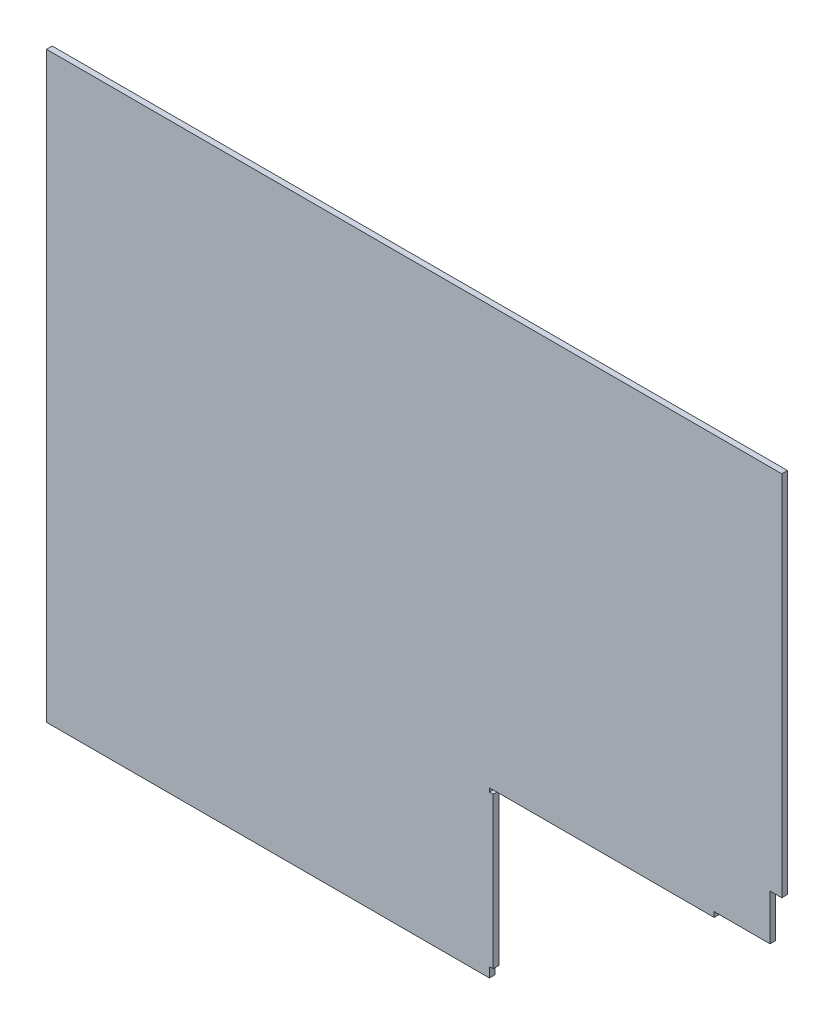
SolidWorks part; units mm, degrees
material "Acrylic (Medium-high impact)"
ref_plane "Front Plane" through (0, 0, 0) normal (0, 0, 1) x (1, 0, 0)
ref_plane "Top Plane" through (0, 0, 0) normal (0, 1, 0) x (1, 0, 0)
ref_plane "Right Plane" through (0, 0, 0) normal (1, 0, 0) x (0, 0, -1)
sketch "Sketch1" plane through (0, 0, 0) normal (0, 0, 1) x (1, 0, 0)
  line L1 (-289.5, -229.5) -> (289.5, -229.5)
  line L2 (-289.5, -229.5) -> (-289.5, 229.5)
  line L3 (-289.5, 229.5) -> (289.5, 229.5)
  line L4 (289.5, -229.5) -> (289.5, 229.5)
  line L5 (-289.5, -229.5) -> (289.5, 229.5) construction
  line L6 (-289.5, 229.5) -> (289.5, -229.5) construction
  point P0 (0, 0)
  dimension "D1" = 579
  dimension "D2" = 459
extrude "Boss-Extrude1" add sketch "Sketch1" along normal mid plane 4.4958
sketch "Sketch2" plane through (0, 0, -2.2479) normal (0, 0, -1) x (-1, 0, 0)
  line L0 (-275.0972, -60.2) -> (-283.75, -60.2) construction
  line L1 (-280.75, -96.2) -> (-280.75, -61.2) construction
  line L2 (-252.237, -96.2) -> (-280.75, -96.2) construction
  line L3 (-236.75, -97.2) -> (-236.75, -99.2) construction
  line L4 (-60.75, -100.2) -> (-283.75, -100.2) construction
  line L5 (-59.75, -100.2) -> (-59.75, -102.2) construction
  line L6 (-60.75, -102.2) -> (-283.75, -102.2) construction
  line L7 (-62.75, -102.45) -> (-62.75, -221.95) construction
  line L8 (-283.75, -222.2) -> (-60.75, -222.2) construction
  line L9 (-59.75, -222.2) -> (-59.75, -224.2) construction
  line L10 (-280.75, -60.2) -> (-289.5, -60.2) construction
  line L11 (-280.75, -96.2) -> (-280.75, -60.2) construction
  line L12 (-236.75, -96.2) -> (-280.75, -96.2) construction
  line L13 (-236.75, -96.2) -> (-236.75, -100.2) construction
  line L14 (-59.75, -100.2) -> (-236.75, -100.2) construction
  line L15 (-59.75, -100.2) -> (-59.75, -102.2) construction
  line L16 (-59.75, -102.2) -> (-62.75, -102.2) construction
  line L17 (-62.75, -102.2) -> (-62.75, -222.2) construction
  line L18 (-62.75, -222.2) -> (-59.75, -222.2) construction
  line L19 (-59.75, -222.2) -> (-59.75, -229.5) construction
  line L20 (-289.5, -60.2) -> (-289.5, -229.5) construction
  line L21 (-289.5, -229.5) -> (-289.5, 229.5) construction
  line L22 (-289.5, -229.5) -> (-59.75, -229.5) construction
  line L23 (-280.25, -59.7) -> (-290, -59.7)
  line L24 (-290, -59.7) -> (-290, -230)
  line L25 (-290, -230) -> (-59.25, -230)
  line L26 (-59.25, -221.7) -> (-59.25, -230)
  line L27 (-62.25, -221.7) -> (-59.25, -221.7)
  line L28 (-62.25, -102.7) -> (-62.25, -221.7)
  line L29 (-59.25, -102.7) -> (-62.25, -102.7)
  line L30 (-59.25, -99.7) -> (-59.25, -102.7)
  line L31 (-59.25, -99.7) -> (-236.25, -99.7)
  line L32 (-236.25, -95.7) -> (-236.25, -99.7)
  line L33 (-236.25, -95.7) -> (-280.25, -95.7)
  line L34 (-280.25, -95.7) -> (-280.25, -59.7)
  dimension "D1" = 0.5
extrude "Cut-Extrude1" cut sketch "Sketch2" against normal up to surface (4.4958 mm away) up to face at (0, 0, 2.2479)
